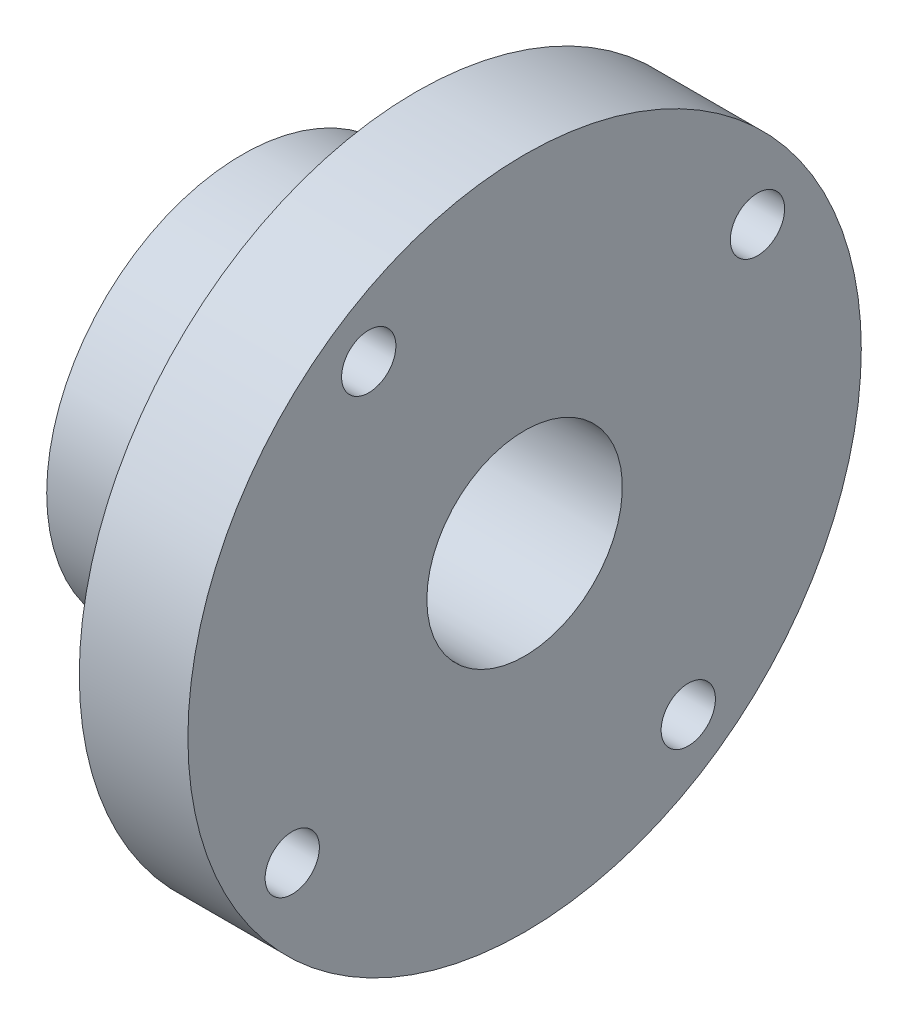
SolidWorks part; units mm, degrees
ref_plane "Plan de face" through (0, 0, 0) normal (0, 0, 1) x (1, 0, 0)
ref_plane "Plan de dessus" through (0, 0, 0) normal (0, 1, 0) x (1, 0, 0)
ref_plane "Plan de droite" through (0, 0, 0) normal (1, 0, 0) x (0, 0, -1)
sketch "Esquisse1" plane through (0, 0, 0) normal (0, 0, 1) x (1, 0, 0)
  line L0 (0, 0) -> (2292.1723, 0) construction
  line L1 (0, 0) -> (0, 7)
  line L2 (0, 7) -> (0.8, 7)
  line L3 (0.8, 7) -> (0.8, 9)
  line L4 (0.8, 9) -> (8.8, 9)
  line L5 (8.8, 9) -> (8.8, 15.5)
  line L6 (8.8, 15.5) -> (13.8, 15.5)
  line L7 (13.8, 15.5) -> (13.8, 0)
  line L8 (0, 0) -> (13.8, 0)
  dimension "D1" = 7
  dimension "D2" = 2
  dimension "D3" = 0.8
  dimension "D4" = 8
  dimension "D5" = 15.5
  dimension "D6" = 5
revolve "Révolution1" add sketch "Esquisse1" angle 360 about L0
hole_wizard "Dégagement M81" positions "Esquisse2" profile "Esquisse3" hole size "M8" standard "Ansi Metric" end condition up to next
sketch "Esquisse2" plane through (0, 0, 0) normal (-1, 0, 0) x (0, 0, 1)
  point P0 (0, 0)
sketch "Esquisse3" plane through (0, 0, 0) normal (0, 1, 0) x (0, 0, 1)
  line L0 (0, 0) -> (0, 13.8)
  line L1 (0, 13.8) -> (4.5, 13.8)
  line L2 (4.5, 13.8) -> (4.5, 0)
  line L5 (4.5, 0) -> (0, 0)
  line L11 (0, -6.35) -> (0, 107.95) construction
  dimension "Diamètre du perçage jusqu'au prochain" = 9
  dimension "Profondeur du perçage jusqu'au prochain" = 13.8
hole_wizard "Trou pour taraudage pour trou taraudé M4x0.71" positions "Esquisse3D2" profile "Esquisse5" hole size "M4x0.7" standard "Ansi Metric"
sketch3d "Esquisse3D2"
  point P0 (4.5664, 0.0445, -8.9999)
sketch "Esquisse5" plane through (4.5664, 0.0445, -8.9999) normal (1, 0, 0) x (0, 1, 0.0049)
  line L0 (0, 0) -> (0, 4.5)
  line L1 (0, 4.5) -> (1.65, 4.5)
  line L2 (1.65, 4.5) -> (1.65, 0)
  line L5 (1.65, 0) -> (0, 0)
  line L11 (0, -6.35) -> (0, 107.95) construction
  dimension "Diamètre du perçage jusqu'au prochain" = 3.3
  dimension "Profondeur du perçage jusqu'au prochain" = 4.5
hole_wizard "Trou pour taraudage pour trou taraudé M3x0.51" positions "Esquisse6" profile "Esquisse7" hole size "M3x0.5" standard "Ansi Metric" end condition up to next
sketch "Esquisse6" plane through (8.8, 0, 0) normal (-1, 0, 0) x (0, 0, 1)
  point P0 (-10.7189, 7.3556)
  point P2 (7.1748, 10.8408)
  point P4 (10.6958, -7.3892)
  point P6 (-7.5342, -10.5941)
  point P8 (0, 0)
  point P9 (0, 0)
  dimension "D1" = 13
  dimension "D2" = 13
  dimension "D3" = 13
  dimension "D4" = 13
  dimension "D5" = 18.23
  dimension "D6" = 18.23
  dimension "D7" = 18.23
  dimension "D8" = 18.23
sketch "Esquisse7" plane through (8.8, 7.3556, -10.7189) normal (0, 1, 0) x (0, 0, 1)
  line L0 (0, 0) -> (0, 5)
  line L1 (0, 5) -> (1.25, 5)
  line L2 (1.25, 5) -> (1.25, 0)
  line L5 (1.25, 0) -> (0, 0)
  line L11 (0, -6.35) -> (0, 107.95) construction
  dimension "Diamètre du perçage jusqu'au prochain" = 2.5
  dimension "Profondeur du perçage jusqu'au prochain" = 5
